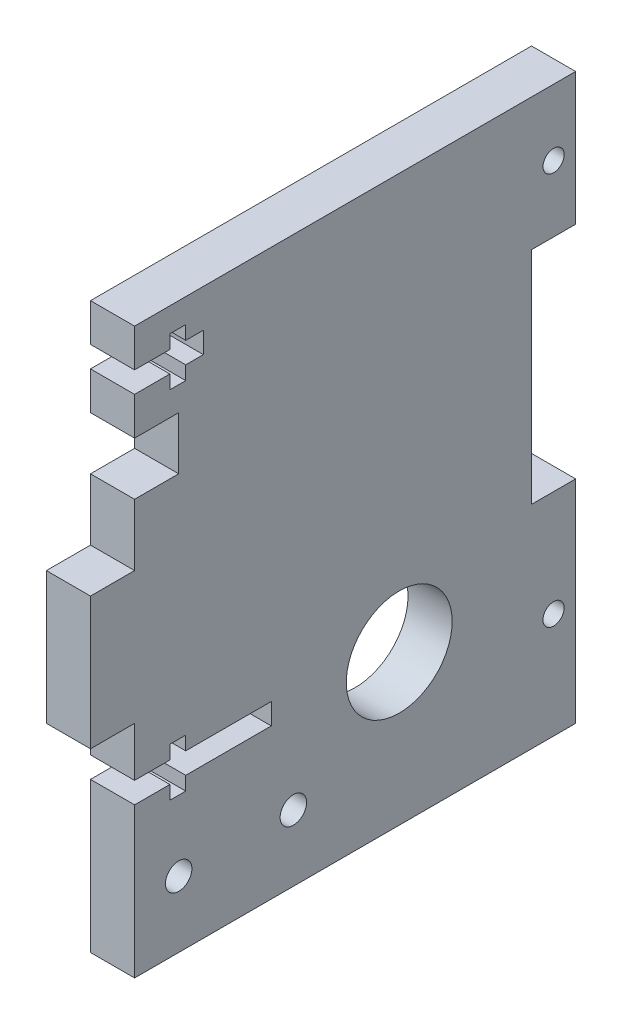
SolidWorks part; units mm, degrees
material "Acrylic (Medium-high impact)"
ref_plane "Front Plane" through (0, 0, 0) normal (0, 0, 1) x (1, 0, 0)
ref_plane "Top Plane" through (0, 0, 0) normal (0, 1, 0) x (1, 0, 0)
ref_plane "Right Plane" through (0, 0, 0) normal (1, 0, 0) x (0, 0, -1)
sketch "Sketch1" plane through (0, 0, 0) normal (1, 0, 0) x (0, 0, -1)
  line L0 (0, 0) -> (-50, 0)
  line L1 (-50, 53) -> (-50, 64)
  line L2 (-50, 25) -> (-50, 0)
  line L3 (-45, 50) -> (-55.472, 50) construction
  line L4 (-20, 64) -> (-20, 0) construction
  line L5 (-38.5, 19.4) -> (-38.5, 17) construction
  line L6 (-50, 25) -> (-55, 25)
  line L7 (-55, 25) -> (-55, 40)
  line L8 (-55, 40) -> (-50, 40)
  line L9 (-50, 40) -> (-50, 47)
  line L10 (-50, 47) -> (-45, 47)
  line L11 (-45, 47) -> (-45, 53)
  line L12 (-45, 53) -> (-50, 53)
  line L13 (-42.5, 19.4) -> (-34.5, 19.4)
  line L14 (-42.5, 19.4) -> (-42.5, 17)
  line L15 (-42.5, 17) -> (-34.5, 17)
  line L16 (-34.5, 19.4) -> (-34.5, 17)
  line L17 (-34.5, 18.2) -> (-42.5, 18.2) construction
  line L18 (-50, 64) -> (0, 64)
  line L19 (0, 64) -> (0, 49)
  line L20 (0, 49) -> (-5, 49)
  line L21 (-5, 49) -> (-5, 24)
  line L22 (-5, 24) -> (0, 24)
  line L23 (0, 24) -> (0, 0)
  circle A0 centre (-20, 17) radius 6
  circle A2 centre (-45, 7.5) radius 1.5
  circle A3 centre (-32, 7.5) radius 1.5
  point P29 (0, 56.5)
  dimension "D9" = 12
  dimension "D15" = 2.4
  dimension "D16" = 6.5
  dimension "D19" = 7.5
  dimension "D1" = 25
  dimension "D2" = 15
  dimension "D3" = 10
  dimension "D4" = 6
  dimension "D5" = 11
  dimension "D6" = 50
  dimension "D7" = 25
  dimension "D8" = 15
  dimension "D12" = 5
  dimension "D13" = 5
  dimension "D14" = 5
  dimension "D17" = 7.5
  dimension "D20" = 5
  dimension "D21" = 30
  dimension "D23" = 2
extrude "Boss-Extrude1" add sketch "Sketch1" along normal blind 5
sketch "Sketch2" plane through (5, 0, 0) normal (1, 0, 0) x (0, 0, -1)
  line L0 (-50, 58.5) -> (0, 58.5) construction
  line L1 (-50, 64) -> (-50, 53) construction
  line L2 (0, 49) -> (0, 64) construction
  line L3 (-50, 59.7) -> (-46, 59.7)
  line L4 (-46, 59.7) -> (-46, 61.25)
  line L5 (-46, 61.25) -> (-44.2, 61.25)
  line L6 (-44.2, 61.25) -> (-44.2, 59.7)
  line L7 (-44.2, 59.7) -> (-42.2, 59.7)
  line L8 (-42.2, 59.7) -> (-42.2, 57.3)
  line L9 (-50, 57.3) -> (-50, 59.7)
  line L10 (-44.2, 57.3) -> (-42.2, 57.3)
  line L11 (-44.2, 55.75) -> (-44.2, 57.3)
  line L12 (-46, 55.75) -> (-44.2, 55.75)
  line L13 (-46, 57.3) -> (-46, 55.75)
  line L14 (-50, 57.3) -> (-46, 57.3)
  line L27 (-44.2, 19.4) -> (-42.2, 19.4)
  line L28 (-42.2, 19.4) -> (-42.2, 17)
  line L29 (-44.2, 20.95) -> (-44.2, 19.4)
  line L30 (-46, 20.95) -> (-44.2, 20.95)
  line L31 (-46, 19.4) -> (-46, 20.95)
  line L32 (-50, 19.4) -> (-46, 19.4)
  line L33 (-50, 17) -> (-50, 19.4)
  line L34 (-50, 17) -> (-46, 17)
  line L35 (-46, 17) -> (-46, 15.45)
  line L36 (-44.2, 15.45) -> (-44.2, 17)
  line L37 (-44.2, 17) -> (-42.2, 17)
  line L38 (-46, 15.45) -> (-44.2, 15.45)
  circle A0 centre (-2.5, 56.5) radius 1.2
  circle A1 centre (-2.5, 12) radius 1.2
  point P15 (-42.2, 58.5)
  dimension "D7" = 2.4
  dimension "D1" = 4
  dimension "D2" = 1.8
  dimension "D3" = 2
  dimension "D4" = 5.5
  dimension "D5" = 2.4
  dimension "D6" = 2
extrude "Cut-Extrude1" cut sketch "Sketch2" against normal through all
